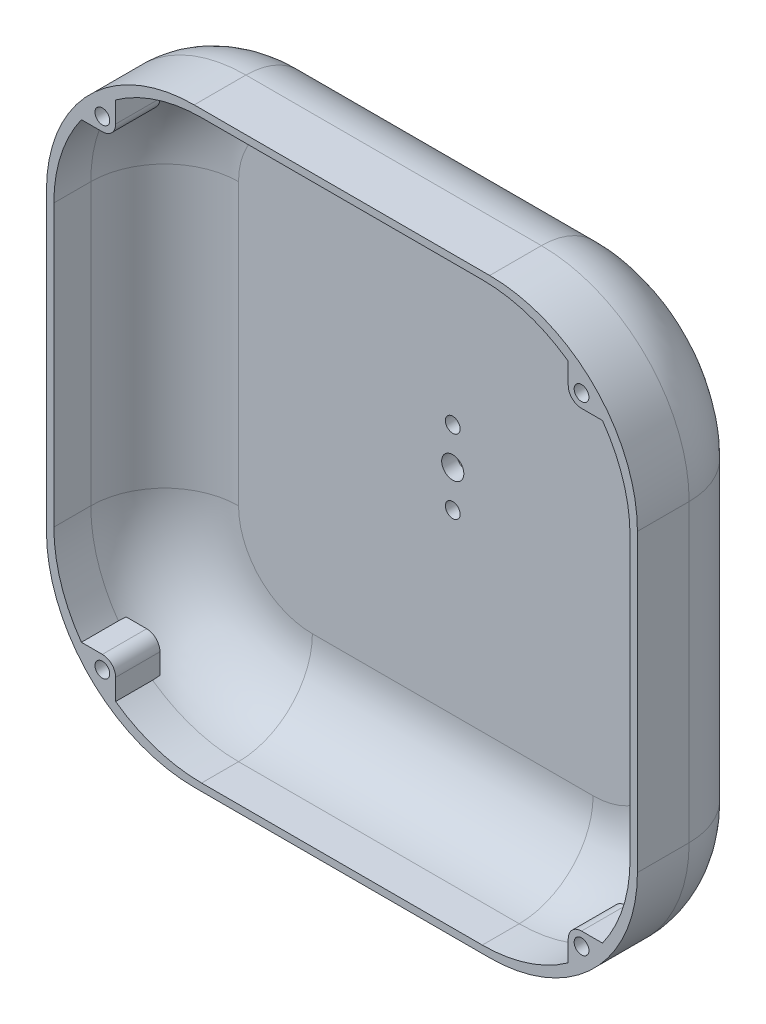
SolidWorks part; units mm, degrees
ref_plane "Front" through (0, 0, 0) normal (0, 0, 1) x (1, 0, 0)
ref_plane "Top" through (0, 0, 0) normal (0, 1, 0) x (1, 0, 0)
ref_plane "Right" through (0, 0, 0) normal (1, 0, 0) x (0, 0, -1)
sketch "Sketch1" plane through (0, 0, 0) normal (0, 0, 1) x (1, 0, 0)
  line L1 (0, 0) -> (80, 0)
  line L2 (0, 0) -> (0, 80)
  line L3 (0, 80) -> (80, 80)
  line L4 (80, 0) -> (80, 80)
  dimension "D1" = 80
  dimension "D2" = 80
extrude "Boss-Extrude1" add sketch "Sketch1" along normal blind 2
sketch "Sketch2" plane through (0, 0, 2) normal (0, 0, 1) x (1, 0, 0)
  line L0 (1, 79) -> (1, 1)
  line L1 (0, 80) -> (80, 80)
  line L2 (0, 80) -> (0, 0)
  line L3 (0, 0) -> (80, 0)
  line L4 (80, 80) -> (80, 0)
  line L5 (1, 1) -> (79, 1)
  line L6 (79, 79) -> (79, 1)
  line L7 (1, 79) -> (79, 79)
  dimension "D1" = 1
extrude "Boss-Extrude2" add sketch "Sketch2" along normal blind 15
fillet "Fillet1" radius 20 4 edges at (79, 1, 9.5) (1, 1, 9.5) (79, 79, 9.5) (1, 79, 9.5)
fillet "Fillet2" radius 10 8 edges at (73.1421, 73.1421, 2) (79, 40, 2) (73.1421, 6.8579, 2) (40, 1, 2) (6.8579, 6.8579, 2) (1, 40, 2) (6.8579, 73.1421, 2) (40, 79, 2)
fillet "Fillet3" radius 20 4 edges at (80, 0, 8.5) (80, 80, 8.5) (0, 80, 8.5) (0, 0, 8.5)
fillet "Fillet4" radius 10 8 edges at (5.8579, 5.8579, 0) (0, 40, 0) (5.8579, 74.1421, 0) (40, 80, 0) (74.1421, 74.1421, 0) (80, 40, 0) (74.1421, 5.8579, 0) (40, 0, 0)
sketch "Sketch3" plane through (0, 0, 17) normal (0, 0, 1) x (1, 0, 0)
  line L0 (72.2928, 5.3721) -> (70.635, 4.1054)
  line L1 (11, 40) -> (54.2273, 40)
  line L2 (11, 59) -> (11, 21) construction
  line L3 (40, 11) -> (40, 48.3049)
  line L4 (21, 11) -> (59, 11) construction
  line L5 (9.365, 4.1054) -> (9.365, 7.565)
  line L6 (7.565, 9.365) -> (3.996, 9.365)
  line L7 (3.996, 9.365) -> (7.7072, 5.3721)
  line L8 (7.7072, 5.3721) -> (9.365, 4.1054)
  line L9 (76.004, 9.365) -> (72.2928, 5.3721)
  line L10 (72.435, 9.365) -> (76.004, 9.365)
  line L11 (70.635, 4.1054) -> (70.635, 7.565)
  line L12 (70.635, 75.8946) -> (70.635, 72.435)
  line L13 (72.435, 70.635) -> (76.004, 70.635)
  line L14 (76.004, 70.635) -> (72.2928, 74.6279)
  line L15 (7.7072, 74.6279) -> (9.365, 75.8946)
  line L16 (3.996, 70.635) -> (7.7072, 74.6279)
  line L17 (7.565, 70.635) -> (3.996, 70.635)
  line L18 (9.365, 75.8946) -> (9.365, 72.435)
  line L19 (72.2928, 74.6279) -> (70.635, 75.8946)
  circle A0 centre (7.565, 7.565) radius 1
  arc A1 (1, 21) -> (21, 1) centre (21, 21) ccw construction
  arc A2 (9.365, 7.565) -> (7.565, 9.365) centre (7.565, 7.565) ccw
  arc A3 (70.635, 7.565) -> (72.435, 9.365) centre (72.435, 7.565) cw
  circle A4 centre (72.435, 7.565) radius 1
  circle A5 centre (72.435, 72.435) radius 1
  arc A6 (70.635, 72.435) -> (72.435, 70.635) centre (72.435, 72.435) ccw
  arc A7 (9.365, 72.435) -> (7.565, 70.635) centre (7.565, 72.435) cw
  circle A8 centre (7.565, 72.435) radius 1
  arc M13 (1, 59) -> (21, 79) centre (21, 59) cw
  arc M15 (59, 79) -> (79, 59) centre (59, 59) cw
  arc M17 (79, 21) -> (59, 1) centre (59, 21) cw
  arc M19 (21, 1) -> (1, 21) centre (21, 21) cw
  dimension "D1" = 2
  dimension "D3" = 0.8
extrude "Boss-Extrude3" add sketch "Sketch3" against normal blind 6 contours A4 L10 A3 L11 M17 | L11 L0 L9 L10 M17 | L5 A2 L6 A0 M19 | L7 L8 L5 L6 M19 | A8 L17 A7 L18 M13 | L18 L15 L16 L17 M13 | L12 A6 L13 A5 M15 | L14 L19 L12 L13 M15
sketch "Sketch4" plane through (0, 0, 0) normal (0, 0, -1) x (-1, 0, 0)
  line L0 (-40, 10) -> (-40, 61.2218)
  line L1 (-60, 10) -> (-20, 10) construction
  line L2 (-70, 40) -> (-30, 40)
  line L3 (-70, 60) -> (-70, 20) construction
  line L5 (-30, 30) -> (-50, 30)
  line L6 (-30, 30) -> (-30, 50)
  line L7 (-30, 50) -> (-50, 50)
  line L8 (-50, 30) -> (-50, 50)
  point P12 (-60.0695, 29.8786)
  point P13 (-40, 30)
  point P14 (-50, 40)
  dimension "D1" = 20
  dimension "D2" = 20
extrude "Boss-Extrude4" add sketch "Sketch4" along normal blind 5 contours L5 L6 L2 L0 | L6 L7 L0 L2 | L8 L2 L0 L7 | L8 L5 L0 L2
sketch "Sketch5" plane through (0, 0, -5) normal (0, 0, -1) x (-1, 0, 0)
  line L0 (-30, 50) -> (-50, 50) construction
  line L1 (-30, 30) -> (-36, 30)
  line L2 (-30, 30) -> (-30, 50)
  line L3 (-30, 50) -> (-36, 50)
  line L4 (-36, 30) -> (-36, 50)
  line L6 (-44, 50) -> (-50, 50)
  line L7 (-44, 50) -> (-44, 30)
  line L8 (-44, 30) -> (-50, 30)
  line L9 (-50, 50) -> (-50, 30)
  dimension "D1" = 6
  dimension "D2" = 6
extrude "Boss-Extrude5" add sketch "Sketch5" along normal blind 20
sketch "Sketch6" plane through (30, 0, 0) normal (-1, 0, 0) x (0, 0, 1)
  line L0 (-25, 30) -> (-25, 50) construction
  line L1 (-25, 50) -> (0, 50) construction
  line L2 (-25, 30) -> (0, 30) construction
  line L3 (-15, 30) -> (-19.7567, 21.1862)
  line L4 (-19.7567, 21.1862) -> (-29.1684, 27.648)
  line L5 (-29.1684, 27.648) -> (-29.1684, 53.8462)
  line L6 (-29.1684, 53.8462) -> (-15, 50)
  arc A0 (-15, 50) -> (-15, 30) centre (-15, 40) ccw
extrude "Cut-Extrude1" cut sketch "Sketch6" against normal blind 23
sketch "Sketch7" plane through (30, 0, 0) normal (-1, 0, 0) x (0, 0, 1)
  circle A1 centre (-15, 40) radius 2
  dimension "D1" = 4
extrude "Cut-Extrude2" cut sketch "Sketch7" against normal blind 23
sketch "Sketch8" plane through (30, 0, 0) normal (-1, 0, 0) x (0, 0, 1)
  circle A0 centre (-15, 40) radius 3.5
  dimension "D1" = 7
extrude "Cut-Extrude3" cut sketch "Sketch8" against normal blind 3
sketch "Sketch9" plane through (0, 0, -5) normal (0, 0, -1) x (-1, 0, 0)
  line L0 (-36, 30) -> (-44, 30) construction
  line L1 (-30, 50) -> (-50, 50) construction
  circle A0 centre (-40, 45) radius 1
  circle A1 centre (-40, 35) radius 1
  point P6 (-40, 30)
  point P10 (-40, 50)
  dimension "D3" = 2
  dimension "D4" = 2
  dimension "D1" = 5
  dimension "D2" = 5
extrude "Cut-Extrude4" cut sketch "Sketch9" against normal blind 18
sketch "Sketch10" plane through (0, 0, -5) normal (0, 0, -1) x (-1, 0, 0)
  line L0 (-30, 50) -> (-50, 50) construction
  line L1 (-50, 50) -> (-50, 30) construction
  circle A0 centre (-40, 40) radius 1.5
  point P2 (0, 0)
  point P5 (-40, 50)
  point P8 (0, 0)
  point P9 (-50, 40)
  dimension "D1" = 3
extrude "Cut-Extrude5" cut sketch "Sketch10" against normal blind 18
sketch "Sketch12" plane through (0, 30, 0) normal (0, -1, 0) x (1, 0, 0)
  line L0 (60, 0) -> (70, 0) construction
  line L1 (66.1642, 0) -> (14.45, 0)
  line L2 (66.1642, 0) -> (66.1642, -32.8052)
  line L3 (66.1642, -32.8052) -> (14.45, -32.8052)
  line L4 (14.45, 0) -> (14.45, -32.8052)
extrude "Cut-Extrude7" cut sketch "Sketch12" against normal blind 37
